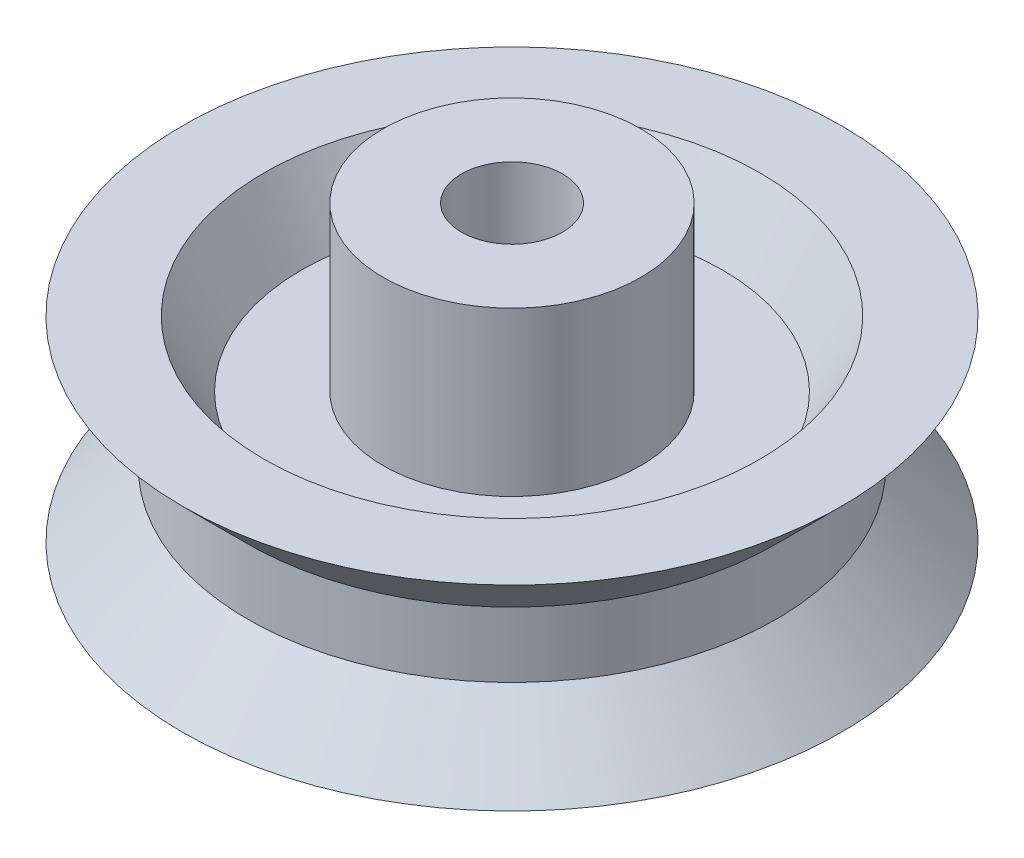
SolidWorks part; units mm, degrees
ref_plane "Plan de face" through (0, 0, 0) normal (0, 0, 1) x (1, 0, 0)
ref_plane "Plan de dessus" through (0, 0, 0) normal (0, 1, 0) x (1, 0, 0)
ref_plane "Plan de droite" through (0, 0, 0) normal (1, 0, 0) x (0, 0, -1)
sketch "Esquisse2" plane through (0, 0, 0) normal (1, 0, 0) x (0, 0, -1)
  line L0 (3.95, 0) -> (3.95, -5)
  line L1 (1.55, -5) -> (3.95, -5)
  line L2 (0, 0) -> (0, 15.5069) construction
  line L14 (3.95, 0) -> (6.45, 0)
  line L15 (6.45, 0) -> (7.6047, -2)
  line L16 (7.6047, -2) -> (10.1047, -2)
  line L17 (10.1047, -2) -> (8.1047, 0)
  line L18 (8.1047, 0) -> (8.1047, 2)
  line L19 (8.1047, 2) -> (10.1047, 4)
  line L20 (10.1047, 4) -> (7.6047, 4)
  line L21 (7.6047, 4) -> (6.45, 2)
  line L22 (6.45, 2) -> (3.95, 2)
  line L23 (3.95, 2) -> (3.95, 7)
  line L24 (3.95, 7) -> (1.55, 7)
  line L25 (1.55, 7) -> (1.55, -5)
  dimension "D1" = 135
  dimension "D2" = 135
  dimension "D3" = 120
  dimension "D4" = 120
  dimension "D5" = 2
  dimension "D6" = 2.5
  dimension "D7" = 2
  dimension "D8" = 5
  dimension "D9" = 2.5
  dimension "D10" = 2.4
  dimension "D11" = 1.55
  dimension "D12" = 5
  dimension "D13" = 2
  dimension "D14" = 12
  dimension "D15" = 2
  dimension "D16" = 2
  dimension "D17" = 2
  dimension "D18" = 5
revolve "Révolution1" add sketch "Esquisse2" angle 360 about L2
